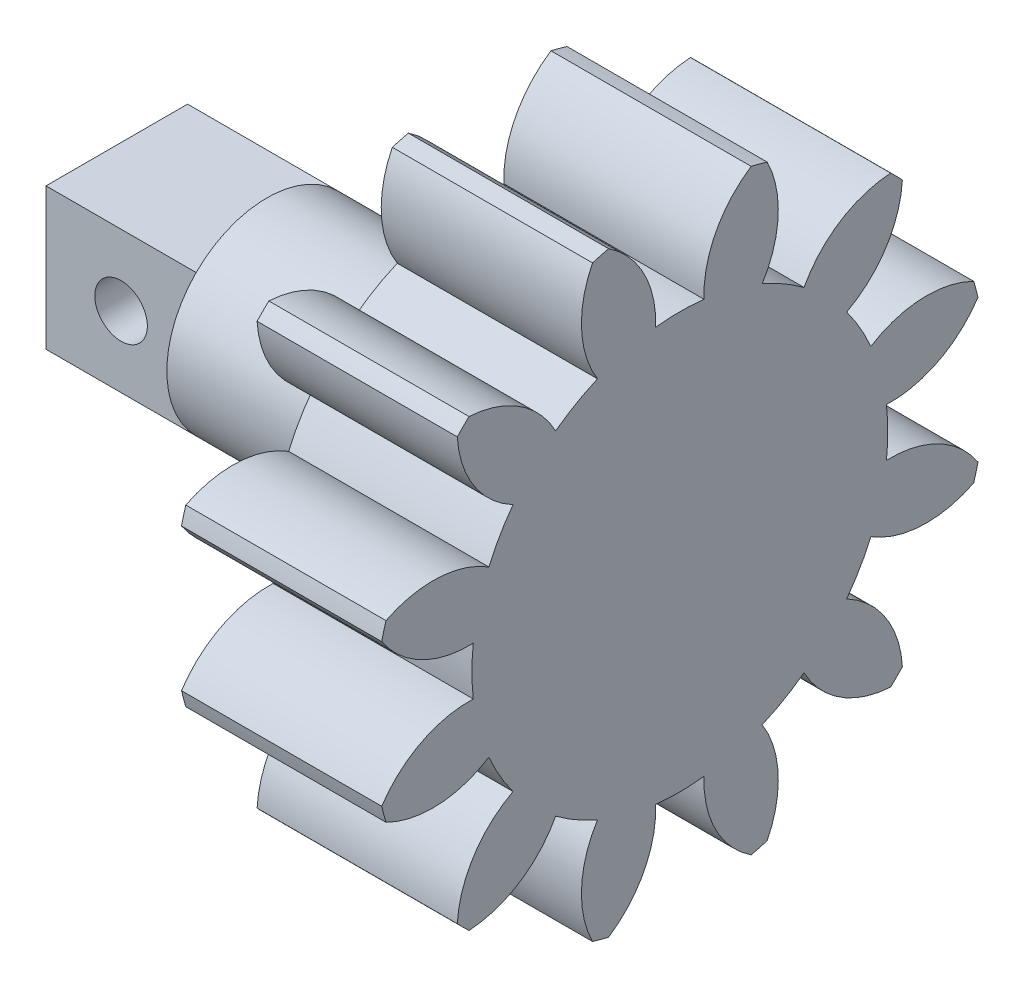
SolidWorks part; units mm, degrees
material "PLA personnalisé"
ref_plane "Plane1" through (0, 0, 0) normal (0, 0, 1) x (1, 0, 0)
ref_plane "Plane2" through (0, 0, 0) normal (0, 1, 0) x (1, 0, 0)
ref_plane "Plane3" through (0, 0, 0) normal (1, 0, 0) x (0, 0, -1)
other "Configuration Table"
sketch "HoldingSke" plane through (0, 0, 0) normal (0, 1, 0) x (1, 0, 0)
  line L0 (0, 0) -> (0.5589, -0.1188)
  line L1 (-15, 0) -> (100, 0) construction
  line L2 (0, 0) -> (-2.1039, 2.3779)
  line L3 (0, 0) -> (-11.863, 4.5341)
  line L4 (0, 0) -> (8.4473, 1.7955)
  line L5 (0, 0) -> (-46.8476, -17.4728)
  line L6 (0, 0) -> (-8.2896, -5.593)
  line L7 (-2.1039, 2.3779) -> (8.6586, 51.2059)
  line L8 (-76.2, 54.61) -> (-74.8, 54.61)
  line L9 (-71.009, 38.7566) -> (-53.1078, 45.2721)
  line L10 (-76.2, 71.12) -> (104.1128, 71.12)
  line L11 (0, 0) -> (-10, 0)
  line L12 (-76.2, 101.6) -> (-76.147, 101.6)
  line L13 (24.9733, 27.94) -> (52.9518, 28.4284)
  line L14 (24.9733, 27.94) -> (24.9743, 27.94)
  line L15 (24.9733, 27.94) -> (100.4006, 29.5858)
  line L16 (-63.627, -1.75) -> (-12.827, -1.75)
  circle A0 centre (0, 0) radius 4.5
  circle A1 centre (0, 0) radius 8.3115
  circle A2 centre (0, 0) radius 37.5
  circle A3 centre (0, 0) radius 4.5
  dimension "MHD" = 16.623
  dimension "Hub_dia" = 75
  dimension "Bore" = 9
  dimension "MBD" = 9
  dimension "Num_teeth" = 12
  dimension "Pitch" = 0.5714
  dimension "Overall_len" = 50
  dimension "Show_teeth" = 12
  dimension "Thickness" = 10
  dimension "OAL" = 50.0001
  dimension "T_dim" = 1.4
  dimension "Ap" = 20
  dimension "H" = 19.05
  dimension "Pitch_radius" = 180.3128
  dimension "Width" = 10
  dimension "Backlash" = 0.053
  dimension "Addendum_fac" = 1
  dimension "Dedendum_fac" = 1.25
  dimension "Clearance_fac" = 0.25
  dimension "Dedendum_add" = 0.001
  dimension "Module" = 1.75
sketch "BasProSke" plane through (0, 0, 0) normal (0, 1, 0) x (1, 0, 0)
  line L0 (-10, 0) -> (60, 0) construction
  line L1 (0, 0) -> (0, 12.25)
  line L2 (0, 0) -> (10, 0)
  line L3 (10, 0) -> (10, 12.25)
  line L4 (10, 12.25) -> (0, 12.25)
  dimension "Thickness" = 10
  dimension "Diameter" = 24.5
revolve "Base-Revolve" add sketch "BasProSke" angle 360 about L0
sketch "TooCutSke" plane through (0, 0, 0) normal (1, 0, 0) x (0, 0, -1)
  line L1 (0, 0) -> (0, 107) construction
  line L2 (0, 0) -> (-1.4632, 10.3976) construction
  line L3 (0, 0) -> (-5.3948, 20.1337) construction
  line L4 (-1.4632, 10.3976) -> (-2.6974, 10.0668) construction
  arc A0 (0.9651, 8.2553) -> (-0.9651, 8.2553) centre (0, 0) ccw
  arc A1 (2.8783, 11.9332) -> (-2.8783, 11.9332) centre (0, 0) ccw
  circle A2 centre (0, 0) radius 10.5 construction
  circle A3 centre (0, 0) radius 9.8668 construction
  arc A4 (-0.9651, 8.2553) -> (-2.8783, 11.9332) centre (-5.1623, 8.4085) ccw
  arc A5 (2.8783, 11.9332) -> (0.9651, 8.2553) centre (5.1623, 8.4085) ccw
  dimension "Root_dia" = 16.623
  dimension "Overcut_dia" = 24.5508
  dimension "Pitch_dia" = 21
  dimension "Base_dia" = 19.7335
  dimension "Flank_rad" = 4.2
  dimension "Half_ang" = 15
  dimension "Half_CT" = 1.2778
extrude "ToothCut" cut sketch "TooCutSke" along normal through all
fillet "Breaks" [suppressed] radius 0.035
fillet "RootFillets" [suppressed] radius 0.4385
pattern_circular "TeethCuts" count 12 every 30 about axis through (-10, 0, 0) along (1, 0, 0) of "ToothCut", "RootFillets", "Breaks"
sketch "HubNeaOneSke" plane through (0, 0, 0) normal (-1, 0, 0) x (0, 0, 1)
  circle A0 centre (0, 0) radius 8.3115
  dimension "Diameter" = 16.623
extrude "HubNearOne" [suppressed] add sketch "HubNeaOneSke" along normal blind 40.0001
sketch "HubNeaBotSke" plane through (0, 0, 0) normal (-1, 0, 0) x (0, 0, 1)
  circle A0 centre (0, 0) radius 8.3115
  dimension "Diameter" = 16.623
extrude "HubNearBoth" [suppressed] add sketch "HubNeaBotSke" along normal blind 20
ref_plane "FarPln" through (10, 0, 0) normal (1, 0, 0) x (0, 0, -1)
sketch "HubFarSke" plane through (10, 0, 0) normal (1, 0, 0) x (0, 0, -1)
  circle A0 centre (0, 0) radius 8.3115
  dimension "Diameter" = 16.623
extrude "HubFar" [suppressed] add sketch "HubFarSke" along normal blind 20
sketch "BorSke" plane through (0, 0, 0) normal (1, 0, 0) x (0, 0, -1)
  circle A0 centre (0, 0) radius 4.5
  dimension "Diameter" = 9
extrude "Bore" cut sketch "BorSke" along normal mid plane 100.0001
sketch "KeySke" plane through (0, 0, 0) normal (1, 0, 0) x (0, 0, -1)
  line L0 (-1.5, 0) -> (-1.5, 5.9)
  line L1 (-1.5, 5.9) -> (1.5, 5.9)
  line L2 (1.5, 5.9) -> (1.5, 0)
  line L3 (0, 0) -> (0, 34) construction
  line L4 (-1.5, 0) -> (1.5, 0)
  dimension "Offset" = 5.9
  dimension "Width" = 3
extrude "Keyway" [suppressed] cut sketch "KeySke" along normal mid plane 100.0001
pattern_circular "Keyway2" [suppressed] count 2 every 90 about axis through (-10, 0, 0) along (1, 0, 0)
sketch "Esquisse4" plane through (0, 0, 0) normal (-1, 0, 0) x (0, 0, 1)
  circle A0 centre (0, 0) radius 16.8497
extrude "Enlèv. mat.-Extru.2" cut sketch "Esquisse4" against normal blind 2
sketch "Esquisse5" plane through (2, 0, 0) normal (-1, 0, 0) x (0, 0, 1)
  circle A0 centre (0, 0) radius 5.0708
extrude "Boss.-Extru.7" add sketch "Esquisse5" against normal blind 8
sketch "Esquisse6" plane through (2, 0, 0) normal (-1, 0, 0) x (0, 0, 1)
  circle A0 centre (0, 0) radius 4
  dimension "D1" = 8
extrude "Boss.-Extru.8" add sketch "Esquisse6" along normal blind 8.5
sketch "Esquisse7" plane through (-6.5, 0, 0) normal (-1, 0, 0) x (0, 0, 1)
  line L0 (4, 0) -> (-4, 0) construction
  line L1 (2.8284, -2.8284) -> (-2.8284, -2.8284)
  line L2 (2.8284, -2.8284) -> (2.8284, 2.8284)
  line L3 (2.8284, 2.8284) -> (-2.8284, 2.8284)
  line L4 (-2.8284, -2.8284) -> (-2.8284, 2.8284)
  line L5 (2.8284, -2.8284) -> (-2.8284, 2.8284) construction
  line L6 (2.8284, 2.8284) -> (-2.8284, -2.8284) construction
  line L7 (-4, 0) -> (0, 0) construction
  line L8 (0, 0) -> (0, 4) construction
  line L9 (0, 4) -> (0, 0) construction
  line L10 (0, 0) -> (3.4051, 3.4051) construction
  line L11 (3.4051, 3.4051) -> (0, 0) construction
  line L12 (0, 0) -> (-3.5303, 3.5303) construction
  circle A0 centre (0, 0) radius 4 construction
  circle A1 centre (0, 0) radius 4 construction
  point P0 (0, 0)
  dimension "D1" = 45
extrude "Boss.-Extru.9" add sketch "Esquisse7" along normal blind 6
sketch "Esquisse8" plane through (0, 0, -2.8284) normal (0, 0, -1) x (-1, 0, 0)
  line L0 (12.5, 0) -> (6.5, 0) construction
  line L1 (12.5, 2.8284) -> (12.5, -2.8284) construction
  line L2 (6.5, -2.8284) -> (6.5, 2.8284) construction
  circle A0 centre (9.5, 0) radius 1.05
  dimension "D1" = 2.1
extrude "Enlèv. mat.-Extru.3" cut sketch "Esquisse8" against normal blind 6
equation "' \"Module@HoldingSke\" = 6.35"
equation "' \"Num_teeth@HoldingSke\" = 12"
equation "' \"Ap@HoldingSke\" =  20"
equation "' \"Ap@HoldingSke\" = 20"
equation "' \"Width@HoldingSke\" = 0.5 * 25.4"
equation "' \"Hub_dia@HoldingSke\"= 1 * 25.4"
equation "' \"Hub_dia@HoldingSke\" = 1 * 25.4"
equation "' \"Overall_len@HoldingSke\" = 1.0 * 25.4"
equation "' \"Bore@HoldingSke\" = 0.75 * 25.4"
equation "' \"T_dim@HoldingSke\" = 0.1 * 25.4"
equation "' \"Width@KeySke\" = 0.25 * 25.4"
equation "' \"Show_teeth@HoldingSke\" = 13"
equation "' \"Backlash@HoldingSke\" = 0.009 * 25.4"
equation "' \"Addendum_fac@HoldingSke\" = 1.0"
equation "' \"Dedendum_fac@HoldingSke\" = 1.25"
equation "' \"Dedendum_add@HoldingSke\" = 0.00005 * 25.4"
equation "' \"Clearance_fac@HoldingSke\" = 0.25"
equation "\"Pitch@HoldingSke\" = 1 / \"Module@HoldingSke\""
equation "\"Overcut_dia@TooCutSke\" = (\"Num_teeth@HoldingSke\" + 2 * \"Addendum_fac@HoldingSke\") / \"Pitch@HoldingSke\" + 0.002 * 25.4"
equation "\"Pitch_dia@TooCutSke\" = \"Num_teeth@HoldingSke\" / \"Pitch@HoldingSke\""
equation "\"Base_dia@TooCutSke\" = \"Num_teeth@HoldingSke\" / \"Pitch@HoldingSke\" * cos((\"Ap@HoldingSke\"  * 3.14159265 / 180))"
equation "\"Root_dia@TooCutSke\" = (\"Num_teeth@HoldingSke\" + 2) / \"Pitch@HoldingSke\" - 2 * (\"Addendum_fac@HoldingSke\" + \"Dedendum_fac@HoldingSke\") / \"Pitch@HoldingSke\" - \"Dedendum_add@HoldingSke\" * 2"
equation "\"Half_ang@TooCutSke\" = 180 / \"Num_teeth@HoldingSke\""
equation "\"Half_CT@TooCutSke\" = \"Num_teeth@HoldingSke\" / \"Pitch@HoldingSke\" * sin((3.14159265 / 2 / \"Num_teeth@HoldingSke\")) / 2 - 7 * \"Backlash@HoldingSke\" / 4"
equation "\"Flank_rad@TooCutSke\" = \"Num_teeth@HoldingSke\" / \"Pitch@HoldingSke\" / 5"
equation "\"Radius@RootFillets\" = \"Clearance_fac@HoldingSke\" / \"Pitch@HoldingSke\" + \"Dedendum_add@HoldingSke\""
equation "\"Break_rad@Breaks\" = 0.02 / \"Pitch@HoldingSke\""
equation "\"Thickness@HoldingSke\" = \"Width@HoldingSke\""
equation "\"OAL@HoldingSke\" = \"Thickness@HoldingSke\""
equation "\"MHD@HoldingSke\" = (\"Num_teeth@HoldingSke\" + 2) / \"Pitch@HoldingSke\" - 2 * (\"Addendum_fac@HoldingSke\" + \"Dedendum_fac@HoldingSke\")  / \"Pitch@HoldingSke\" - \"Dedendum_add@HoldingSke\" * 2"
equation "\"MBD@HoldingSke\" = (\"Num_teeth@HoldingSke\" + 2) / \"Pitch@HoldingSke\" - 2 * (\"Addendum_fac@HoldingSke\" + \"Dedendum_fac@HoldingSke\")  / \"Pitch@HoldingSke\" - \"Dedendum_add@HoldingSke\" * 2 - 0.002 * 25.4"
equation "\"MHD@HoldingSke\" = ((sgn( \"MHD@HoldingSke\" - \"Hub_dia@HoldingSke\" )-1)*( \"MHD@HoldingSke\" - \"Hub_dia@HoldingSke\" ))/-2+ \"Hub_dia@HoldingSke\""
equation "\"MBD@HoldingSke\" = ((sgn( \"MBD@HoldingSke\" - \"Bore@HoldingSke\" )-1)*( \"MBD@HoldingSke\" - \"Bore@HoldingSke\" ))/-2+ \"Bore@HoldingSke\""
equation "\"OAL@HoldingSke\" = ((sgn( \"OAL@HoldingSke\" - \"Overall_len@HoldingSke\" )+1)*( \"OAL@HoldingSke\" - \"Overall_len@HoldingSke\" ))/2 + \"Overall_len@HoldingSke\" + 0.000002 * 25.4"
equation "\"Num_teeth@TeethCuts\" = int( \"Show_teeth@HoldingSke\" ) + 1"
equation "\"Num_teeth@TeethCuts\" = ((sgn( \"Num_teeth@TeethCuts\" - \"Num_teeth@HoldingSke\" )-1)*( \"Num_teeth@TeethCuts\" - \"Num_teeth@HoldingSke\" ))/-2+ \"Num_teeth@HoldingSke\""
equation "\"Num_teeth@TeethCuts\" = ((sgn( \"Num_teeth@TeethCuts\" - 2.0)+1)*( \"Num_teeth@TeethCuts\" - 2.0))/2 +2.0"
equation "\"Angle@TeethCuts\" = 360.0 / \"Num_teeth@HoldingSke\""
equation "\"Diameter@BasProSke\" = (\"Num_teeth@HoldingSke\" + 2 * \"Addendum_fac@HoldingSke\") / \"Pitch@HoldingSke\""
equation "\"Thickness@BasProSke\"  = \"Thickness@HoldingSke\""
equation "' \"Fillet_rad@BasProSke\" =  \"Thickness@HoldingSke\" * 0.05"
equation "' \"Fillet_rad@BasProSke\" = \"Thickness@HoldingSke\" * 0.05"
equation "\"MHD@HoldingSke\" = ((sgn( \"MHD@HoldingSke\" - \"Root_dia@TooCutSke\" )-1)*( \"MHD@HoldingSke\" - \"Root_dia@TooCutSke\" ))/-2+ \"Root_dia@TooCutSke\""
equation "\"Diameter@HubNeaOneSke\" = \"MHD@HoldingSke\""
equation "\"Length@HubNearOne\" = \"OAL@HoldingSke\" - \"Thickness@BasProSke\""
equation "\"Diameter@HubNeaBotSke\" = \"MHD@HoldingSke\""
equation "\"Length@HubNearBoth\" = ( \"OAL@HoldingSke\" - \"Thickness@BasProSke\" ) / 2.0"
equation "\"Thickness@FarPln\" = \"Thickness@BasProSke\""
equation "\"Diameter@HubFarSke\" = \"MHD@HoldingSke\""
equation "\"Length@HubFar\" = ( \"OAL@HoldingSke\" - \"Thickness@BasProSke\" ) / 2.0"
equation "\"Diameter@BorSke\" = \"MBD@HoldingSke\""
equation "\"D1@Bore\" = \"OAL@HoldingSke\" * 2.0"
equation "\"D1@Keyway\" = \"OAL@HoldingSke\" * 2.0"
equation "\"Offset@KeySke\" = \"T_dim@HoldingSke\" + \"MBD@HoldingSke\" / 2.0"
